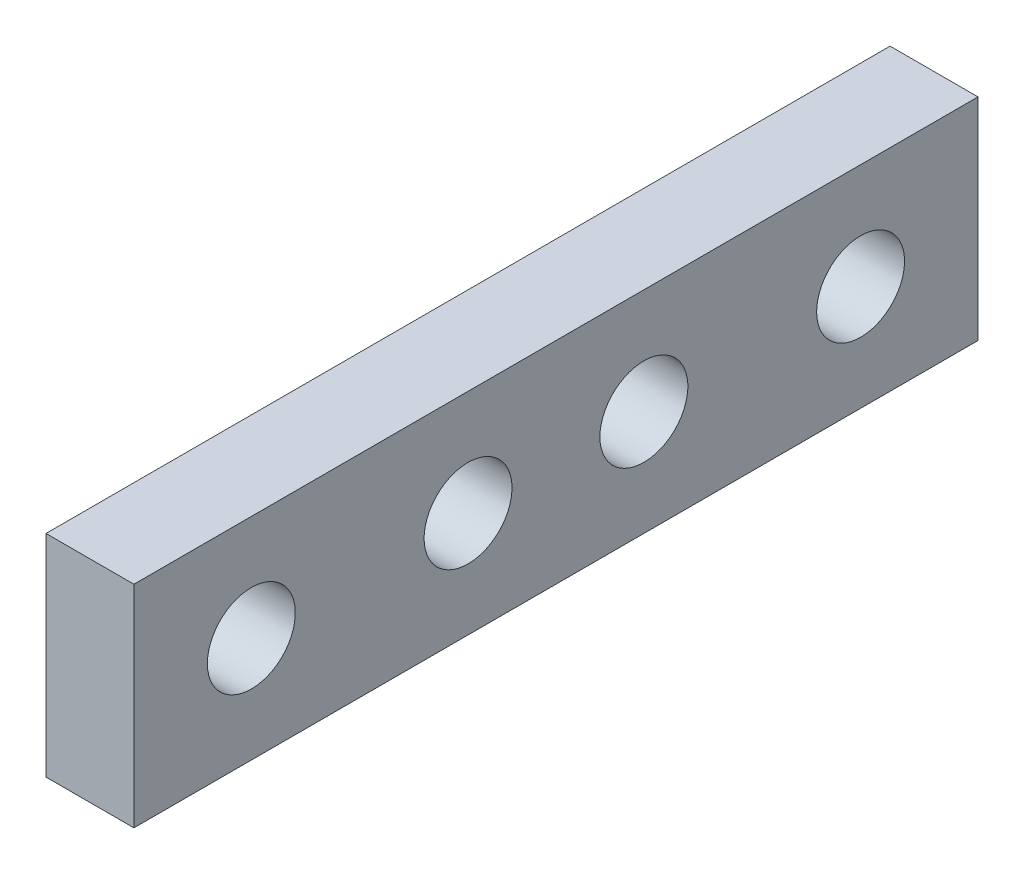
SolidWorks part; units mm, degrees
ref_plane "Front Plane" through (0, 0, 0) normal (0, 0, 1) x (1, 0, 0)
ref_plane "Top Plane" through (0, 0, 0) normal (0, 1, 0) x (1, 0, 0)
ref_plane "Right Plane" through (0, 0, 0) normal (1, 0, 0) x (0, 0, -1)
sketch "Sketch1" plane through (0, 0, 0) normal (0, 0, 1) x (1, 0, 0)
  line L1 (-1.5875, -3.81) -> (1.5875, -3.81)
  line L2 (-1.5875, -3.81) -> (-1.5875, 3.81)
  line L3 (-1.5875, 3.81) -> (1.5875, 3.81)
  line L4 (1.5875, -3.81) -> (1.5875, 3.81)
  line L5 (-1.5875, -3.81) -> (1.5875, 3.81) construction
  line L6 (-1.5875, 3.81) -> (1.5875, -3.81) construction
  point P0 (0, 0)
  dimension "D1" = 3.175
  dimension "D2" = 7.62
extrude "Boss-Extrude1" add sketch "Sketch1" along normal blind 15.24
mirror "Mirror1" about plane through (0, 0, 0) normal (0, 0, 1) of "Boss-Extrude1"
sketch "Sketch2" plane through (0, 3.81, 0) normal (0, 1, 0) x (1, 0, 0)
  line L0 (0, 11) -> (0, -11) construction
  circle A0 centre (0, 11) radius 1.1303
  circle A1 centre (0, -11) radius 1.1303
  dimension "D2" = 2.2606
  dimension "D3" = 2.2606
  dimension "D1" = 22
extrude "Cut-Extrude1" [suppressed] cut sketch "Sketch2" against normal through all
sketch "Sketch3" plane through (-1.5875, 0, 0) normal (-1, 0, 0) x (0, 0, 1)
  line L0 (-3.175, 0) -> (3.175, 0) construction
  circle A0 centre (-3.175, 0) radius 1.5875
  circle A1 centre (3.175, 0) radius 1.5875
  dimension "D2" = 3.175
  dimension "D3" = 3.175
  dimension "D1" = 6.35
extrude "Cut-Extrude2" cut sketch "Sketch3" against normal through all
sketch "Sketch5" plane through (-1.5875, 0, 0) normal (-1, 0, 0) x (0, 0, 1)
  line L0 (-11, 0) -> (11, 0) construction
  circle A0 centre (-11, 0) radius 1.5875
  circle A1 centre (11, 0) radius 1.5875
  dimension "D2" = 3.175
  dimension "D3" = 3.175
  dimension "D1" = 22
extrude "Cut-Extrude4" cut sketch "Sketch5" against normal through all
